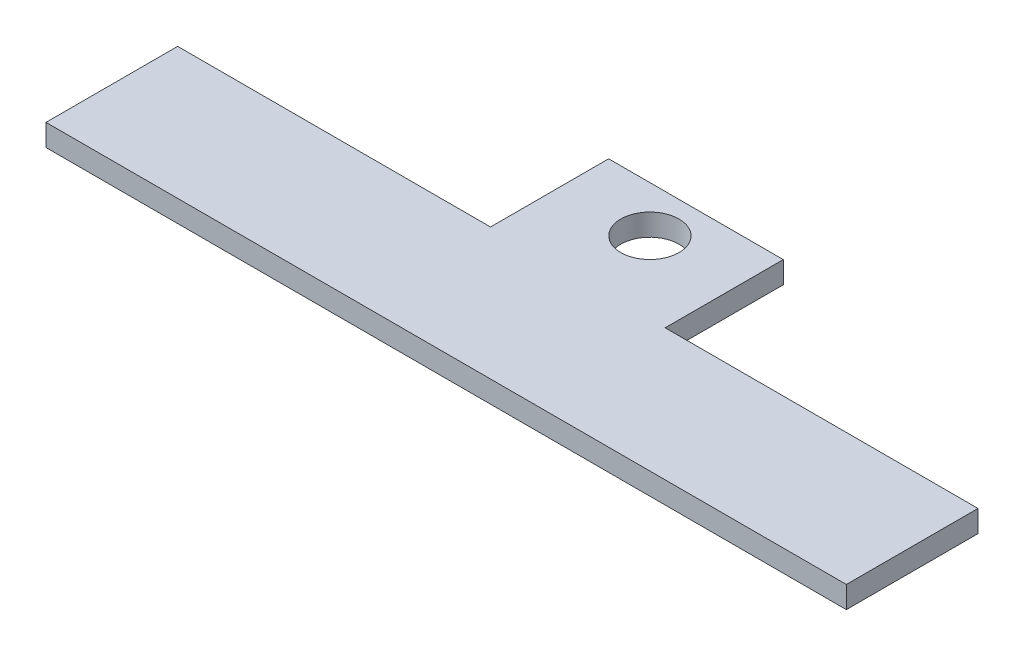
SolidWorks part; units mm, degrees
ref_plane "Спереди" through (0, 0, 0) normal (0, 0, 1) x (1, 0, 0)
ref_plane "Сверху" through (0, 0, 0) normal (0, 1, 0) x (1, 0, 0)
ref_plane "Справа" through (0, 0, 0) normal (1, 0, 0) x (0, 0, -1)
sketch "Эскиз1" plane through (0, 0, 0) normal (0, 1, 0) x (1, 0, 0)
  line L0 (0, 9.0465) -> (21.5, 9.0465)
  line L1 (0, 0) -> (55, 0)
  line L2 (0, 0) -> (0, 9.0465)
  line L4 (55, 0) -> (55, 9.0465)
  line L5 (21.5, 9.0465) -> (21.5, 17.1649)
  line L6 (21.5, 17.1649) -> (33.5, 17.1649)
  line L7 (33.5, 17.1649) -> (33.5, 9.0465)
  line L8 (33.5, 9.0465) -> (55, 9.0465)
  line L9 (27.5, 0) -> (27.5, 34.3298) construction
  circle A2 centre (27.5, 14) radius 2
  point P11 (0, 0)
  point P13 (27.5, 17.1649)
extrude "Бобышка-Вытянуть1" add sketch "Эскиз1" along normal blind 1.5
